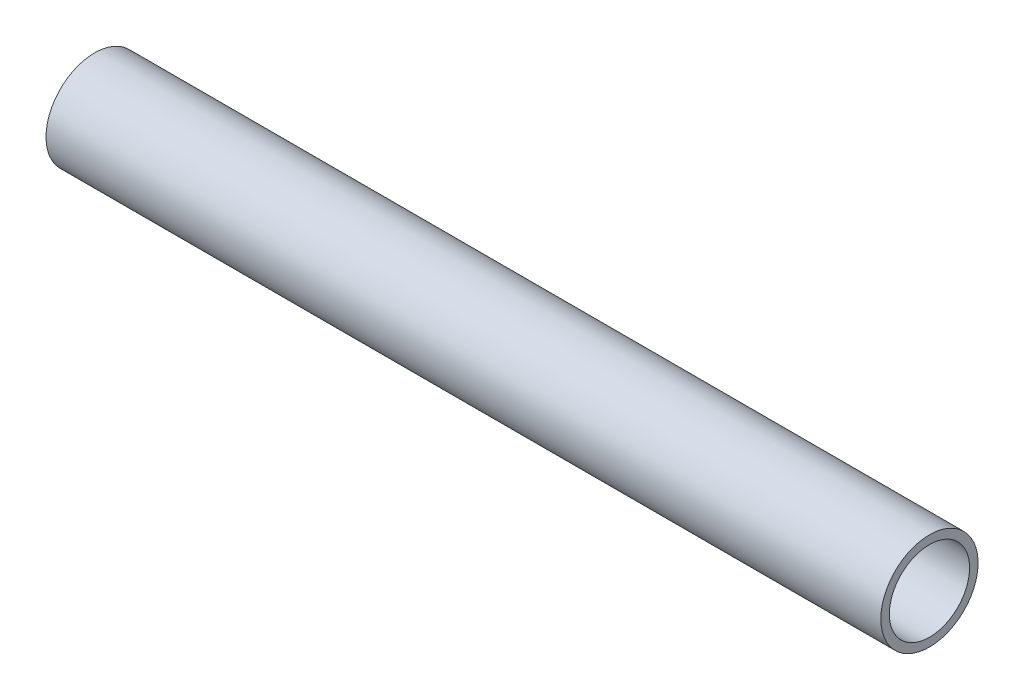
SolidWorks part; units mm, degrees
ref_plane "Front Plane" through (0, 0, 0) normal (0, 0, 1) x (1, 0, 0)
ref_plane "Top Plane" through (0, 0, 0) normal (0, 1, 0) x (1, 0, 0)
ref_plane "Right Plane" through (0, 0, 0) normal (1, 0, 0) x (0, 0, -1)
sketch "Sketch1" plane through (0, 0, 0) normal (0, 0, 1) x (1, 0, 0)
  line L0 (0, 23.2958) -> (0, -16.0632) construction
  line L1 (-17.6611, 0) -> (470.8766, 0) construction
  line L3 (0, 21.082) -> (361.95, 21.082)
  line L4 (0, 21.082) -> (0, 17.399)
  line L5 (0, 17.399) -> (361.95, 17.399)
  line L6 (361.95, 21.082) -> (361.95, 17.399)
  point P9 (470.8766, 0)
  dimension "D1" = 34.798
  dimension "D2" = 42.164
  dimension "D3" = 361.95
revolve "Revolve1" add sketch "Sketch1" angle 360 about L1
